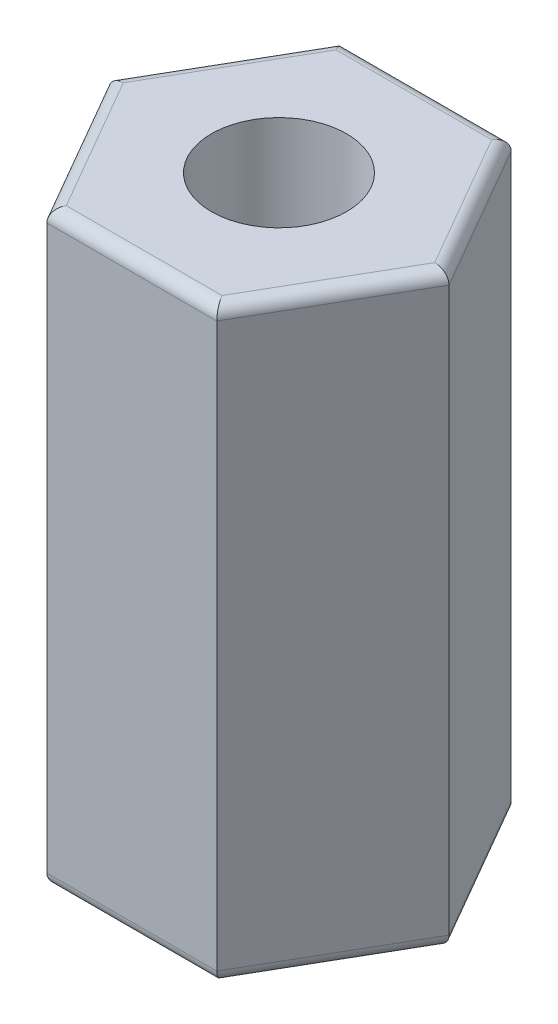
SolidWorks part; units mm, degrees
material "201.0-T43 Molde de fundição com isolamento (SS)"
ref_plane "Plano frontal" through (0, 0, 0) normal (0, 0, 1) x (1, 0, 0)
ref_plane "Plano superior" through (0, 0, 0) normal (0, 1, 0) x (1, 0, 0)
ref_plane "Plano direito" through (0, 0, 0) normal (1, 0, 0) x (0, 0, -1)
sketch "Esboço1" plane through (0, 0, 0) normal (0, 1, 0) x (1, 0, 0)
  line L1 (2.7482, 0) -> (1.3741, 2.38)
  line L2 (1.3741, 2.38) -> (-1.3741, 2.38)
  line L3 (-1.3741, 2.38) -> (-2.7482, 0)
  line L4 (-2.7482, 0) -> (-1.3741, -2.38)
  line L5 (-1.3741, -2.38) -> (1.3741, -2.38)
  line L6 (1.3741, -2.38) -> (2.7482, 0)
  circle A0 centre (0, 0) radius 2.38 construction
  dimension "D1" = 4.76
extrude "Ressalto-extrusão1" add sketch "Esboço1" along normal blind 9.5
fillet "Filete1" radius 0.2 12 edges at (0, 9.5, -2.38) (-2.0611, 9.5, -1.19) (-2.0611, 9.5, 1.19) (0, 9.5, 2.38) (2.0611, 9.5, 1.19) (2.0611, 9.5, -1.19) (0, 0, 2.38) (-2.0611, 0, 1.19) (-2.0611, 0, -1.19) (0, 0, -2.38) (2.0611, 0, -1.19) (2.0611, 0, 1.19)
sketch "Esboço2" plane through (0, 0, 0) normal (0, -1, 0) x (1, 0, 0)
  circle A0 centre (0, 0) radius 1.0922
  dimension "D1" = 2.1844
sketch "Esboço3" plane through (0, 9.5, 0) normal (0, 1, 0) x (1, 0, 0)
  circle A0 centre (0, 0) radius 1.0922
extrude "Corte-extrusão1" cut sketch "Esboço3" against normal blind 4.76
extrude "Corte-extrusão2" cut sketch "Esboço2" against normal through all
